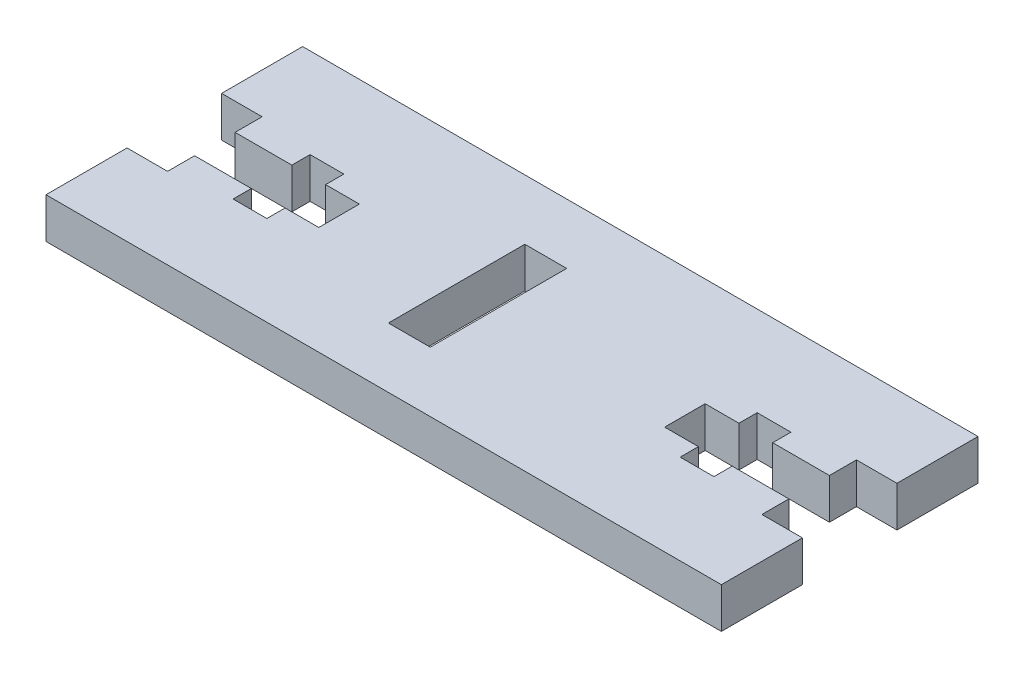
SolidWorks part; units mm, degrees
ref_plane "Front Plane" through (0, 0, 0) normal (0, 0, 1) x (1, 0, 0)
ref_plane "Top Plane" through (0, 0, 0) normal (0, 1, 0) x (1, 0, 0)
ref_plane "Right Plane" through (0, 0, 0) normal (1, 0, 0) x (0, 0, -1)
sketch "Sketch2" plane through (0, 0, 0) normal (0, 1, 0) x (1, 0, 0)
  line L1 (0, 0) -> (50, 0)
  line L2 (0, 0) -> (0, 19)
  line L3 (0, 19) -> (50, 19)
  line L4 (50, 0) -> (50, 19)
  dimension "D1" = 50
  dimension "D2" = 19
extrude "Boss-Extrude1" add sketch "Sketch2" along normal blind 3
sketch "Sketch3" plane through (0, 3, 0) normal (0, 1, 0) x (1, 0, 0)
  line L0 (0, 13) -> (3, 13)
  line L1 (0, 19) -> (0, 0) construction
  line L2 (3, 13) -> (3, 11)
  line L3 (3, 11) -> (7.2, 11)
  line L4 (7.2, 11) -> (7.2, 12.35)
  line L7 (12.2, 8) -> (9.7, 8)
  line L8 (9.7, 8) -> (9.7, 6.65)
  line L9 (9.7, 6.65) -> (7.2, 6.65)
  line L10 (7.2, 6.65) -> (7.2, 8)
  line L11 (7.2, 8) -> (3, 8)
  line L12 (3, 8) -> (3, 6)
  line L13 (3, 6) -> (0, 6)
  line L14 (0, 6) -> (0, 13)
  line L15 (7.2, 12.35) -> (9.7, 12.35)
  line L16 (9.7, 12.35) -> (9.7, 11)
  line L17 (9.7, 11) -> (12.2, 11)
  line L18 (12.2, 11) -> (12.2, 8)
  line L19 (50, 9.5) -> (0, 9.5) construction
  line L20 (50, 0) -> (50, 19) construction
  line L21 (5.1, 11) -> (5.1, 8) construction
  point P24 (5.1, 9.5)
  dimension "D1" = 5.7
  dimension "D2" = 3
  dimension "D3" = 3
  dimension "D4" = 2.5
  dimension "D5" = 2.5
  dimension "D6" = 4.2
  dimension "D7" = 3
  dimension "D8" = 7
extrude "Cut-Extrude1" cut sketch "Sketch3" against normal through all
ref_plane "Plane1" through (25, 0, 0) normal (1, 0, 0) x (0, 0, -1)
mirror "Mirror1" about plane through (25, 0, 0) normal (1, 0, 0) of "Cut-Extrude1"
sketch "Sketch4" plane through (0, 3, 0) normal (0, 1, 0) x (1, 0, 0)
  line L0 (0, 13) -> (0, 6) construction
  line L1 (20.9, 14.55) -> (24, 14.55)
  line L2 (20.9, 14.55) -> (20.9, 4.45)
  line L3 (20.9, 4.45) -> (24, 4.45)
  line L4 (24, 14.55) -> (24, 4.45)
  line L5 (0, 9.5) -> (49.4461, 9.5) construction
  line L6 (22.45, 14.55) -> (22.45, 4.45) construction
  line L7 (12.2, 8) -> (12.2, 11) construction
  point P12 (22.45, 9.5)
  dimension "D1" = 3.1
  dimension "D2" = 10.1
  dimension "D3" = 8.7
extrude "Cut-Extrude2" cut sketch "Sketch4" against normal through all
